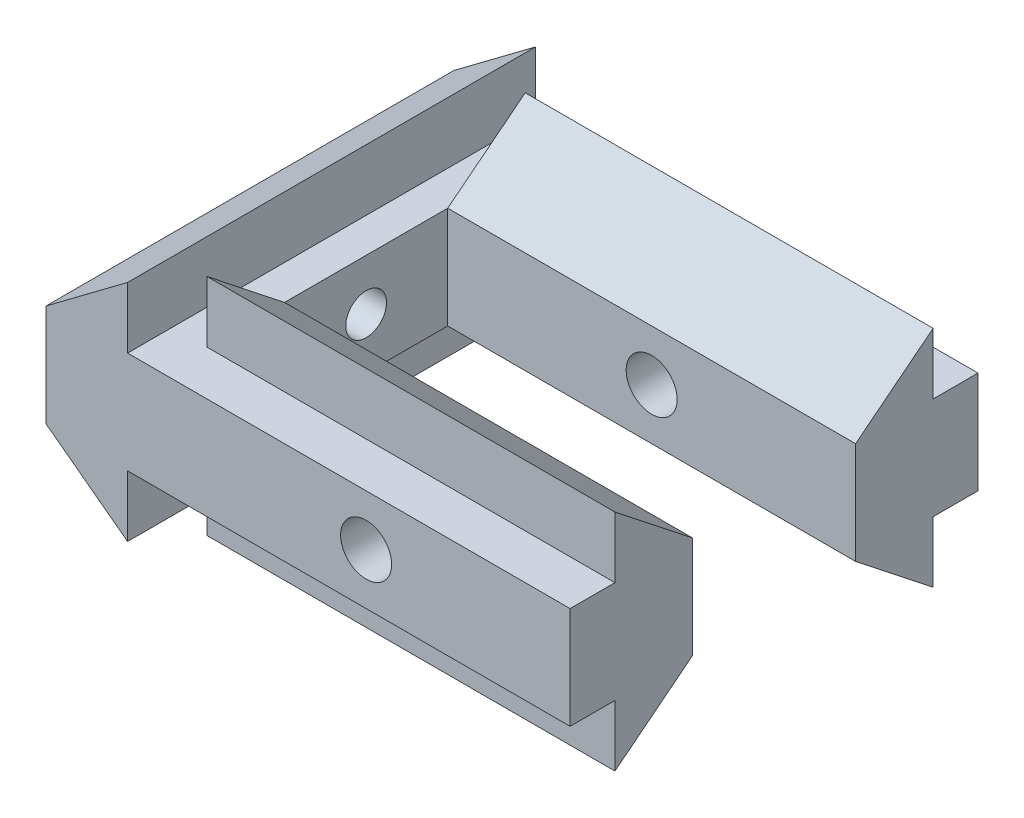
SolidWorks part; units mm, degrees
ref_plane "Plan de face" through (0, 0, 0) normal (0, 0, 1) x (1, 0, 0)
ref_plane "Plan de dessus" through (0, 0, 0) normal (0, 1, 0) x (1, 0, 0)
ref_plane "Plan de droite" through (0, 0, 0) normal (1, 0, 0) x (0, 0, -1)
sketch "ProfileRainureEsquisse" plane through (0, 0, 0) normal (0, 0, 1) x (1, 0, 0)
  line L0 (0, 0) -> (0, 5)
  line L1 (0, 5) -> (4, 8)
  line L2 (0, 0) -> (4, -3)
  line L3 (4, 8) -> (4, 5)
  line L4 (4, 5) -> (5.6958, 5)
  line L5 (5.6958, 5) -> (5.6958, 0)
  line L6 (5.6958, 0) -> (4, 0)
  line L7 (4, 0) -> (4, -3)
  dimension "D1" = 4
  dimension "D2" = 5.6958
  dimension "D3" = 5
  dimension "D4" = 8
extrude "Boss.-Extru.1" add sketch "ProfileRainureEsquisse" along normal blind 20
sketch "Esquisse1" plane through (5.6958, 0, 0) normal (1, 0, 0) x (0, 0, -1)
  line L0 (-20, 0) -> (-20, 5) construction
  circle A0 centre (-10, 2.5) radius 1
  point P2 (-20, 2.5)
  point P7 (-20, 2.5)
  point P10 (-20, 2.5)
  dimension "D1" = 2
  dimension "D2" = 10
extrude "Enlèv. mat.-Extru.1" cut sketch "Esquisse1" against normal through all
sketch "Esquisse2" plane through (5.6958, 0, 0) normal (1, 0, 0) x (0, 0, -1)
  line L0 (-14, 0) -> (-14, 5)
  line L1 (-14, 5) -> (-17.8, 8)
  line L2 (-17.8, 8) -> (-17.8, 5)
  line L3 (-17.8, -3) -> (-14, 0)
  line L4 (-6, 5) -> (-6, 0)
  line L5 (-6, 0) -> (-2.2, -3)
  line L6 (-2.2, 8) -> (-2.2, 5)
  line L7 (-2.2, 8) -> (-6, 5)
  line L8 (-20, 5) -> (0, 5) construction
  line L9 (-17.8, 5) -> (-20, 5)
  line L10 (-20, 5) -> (0, 5) construction
  line L11 (-20, 5) -> (-20, 0)
  line L12 (-20, 0) -> (-17.8, 0)
  line L13 (-17.8, 0) -> (-17.8, -3)
  line L15 (-2.2, 5) -> (0, 5)
  line L16 (0, 5) -> (0, 0)
  line L17 (-20, 0) -> (0, 0) construction
  line L18 (0, 0) -> (-2.2, 0)
  line L19 (-20, 0) -> (0, 0) construction
  line L20 (-2.2, 0) -> (-2.2, -3)
  line L21 (-20, 0) -> (-20, 5) construction
  line L22 (0, 0) -> (0, 5) construction
  dimension "D1" = 2.2
  dimension "D2" = 3.8
  dimension "D3" = 8
extrude "Boss.-Extru.2" add sketch "Esquisse2" along normal blind 20
sketch "Esquisse3" plane through (0, 0, 20) normal (0, 0, 1) x (1, 0, 0)
  line L0 (25.6958, 5) -> (25.6958, 0) construction
  circle A0 centre (15.6958, 2.5) radius 1.25
  point P4 (25.6958, 2.5)
  dimension "D1" = 2.5
  dimension "D2" = 10
extrude "Enlèv. mat.-Extru.2" cut sketch "Esquisse3" against normal through all
